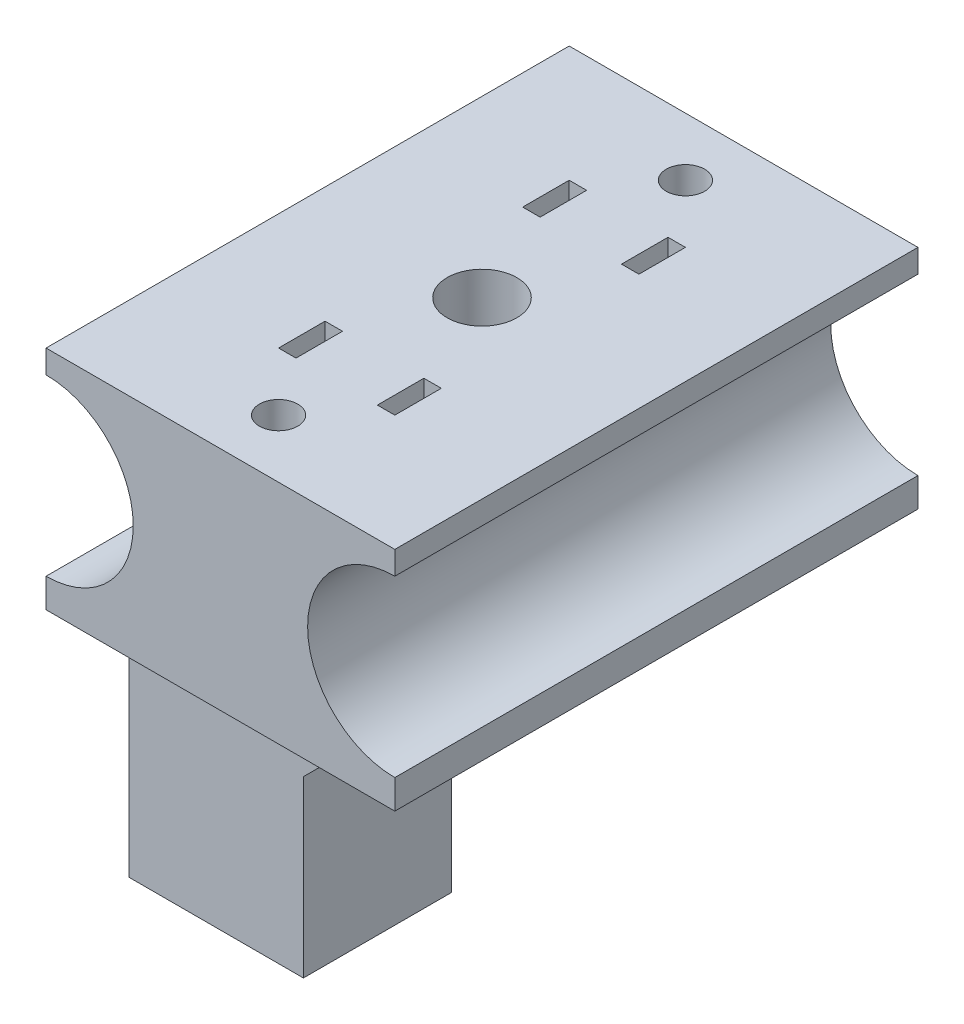
SolidWorks part; units mm, degrees
material "ABS"
ref_plane "Front Plane" through (0, 0, 0) normal (0, 0, 1) x (1, 0, 0)
ref_plane "Top Plane" through (0, 0, 0) normal (0, 1, 0) x (1, 0, 0)
ref_plane "Right Plane" through (0, 0, 0) normal (1, 0, 0) x (0, 0, -1)
sketch "Sketch1" plane through (0, 0, 0) normal (0, 0, 1) x (1, 0, 0)
  line L0 (15, 0) -> (-15, 0) construction
  line L5 (-15, 7.5) -> (-15, 9.5)
  line L6 (-15, 9.5) -> (15, 9.5)
  line L7 (15, 7.5) -> (15, 9.5)
  line L9 (-15, -7.5) -> (-15, -10)
  line L10 (-15, -10) -> (15, -10)
  line L11 (15, -7.5) -> (15, -10)
  arc A0 (15, 7.5) -> (15, -7.5) centre (15, 0) ccw
  arc A1 (-15, -7.5) -> (-15, 7.5) centre (-15, 0) ccw
  point P8 (0, 0)
  dimension "D2" = 15
  dimension "D1" = 30
  dimension "D3" = 2.5
  dimension "D4" = 2
extrude "Boss-Extrude1" add sketch "Sketch1" along normal mid plane 45
sketch "Sketch3" plane through (0, 0, 0) normal (0, 0, 1) x (1, 0, 0)
  line L0 (0, 9.5) -> (0, -10)
  line L1 (0, -10) -> (8, -10)
  line L2 (8, -10) -> (8, -3.25)
  line L3 (8, -3.25) -> (6, -3.25)
  line L4 (6, -3.25) -> (6, 2.75)
  line L5 (6, 2.75) -> (8, 2.75)
  line L6 (8, 2.75) -> (8, 9.5)
  line L7 (8, 9.5) -> (0, 9.5)
  line L8 (15, 9.5) -> (-15, 9.5) construction
  line L9 (-15, -10) -> (15, -10) construction
  dimension "D1" = 6
  dimension "D2" = 8
  dimension "D3" = 6
revolve "Cut-Revolve1" [suppressed] cut sketch "Sketch3" angle 360 about L0
hole_wizard "M4x0.7 Tapped Hole2" positions "Sketch5" profile "Sketch4" tap size "M4x0.7" standard "ANSI Metric" end condition through all
sketch "Sketch5" plane through (0, -10, 0) normal (0, -1, 0) x (-1, 0, 0)
  line L0 (0, 17.5) -> (0, -17.5) construction
  line L2 (15, -22.5) -> (-15, -22.5) construction
  point P0 (0, -17.5)
  point P2 (0, 17.5)
  dimension "D1" = 5
sketch "Sketch4" plane through (0, -10, 17.5) normal (1, 0, 0) x (0, 0, -1)
  line L0 (0, 0) -> (0, 19.5)
  line L1 (0, 19.5) -> (1.65, 19.5)
  line L2 (1.65, 19.5) -> (1.65, 0)
  line L5 (1.65, 0) -> (0, 0)
  line L11 (0, -6.35) -> (0, 107.95) construction
  dimension "Thru Tap Drill Dia." = 3.3
  dimension "Thru Tap Drill Depth" = 19.5
cosmetic thread "Hole Thread1" parameters "D2"=4
cosmetic thread "Hole Thread2" parameters "D2"=4
sketch "Sketch7" plane through (0, 0, 0) normal (0, 0, 1) x (1, 0, 0)
  line L0 (-15, -7.5) -> (-24, -7.5)
  line L1 (-24, -7.5) -> (-24, -42.5)
  line L5 (8.5, -10) -> (-15, -10)
  line L6 (-15, -10) -> (-15, -7.5)
  line L7 (-24, -42.5) -> (-9, -42.5)
  line L8 (-9, -42.5) -> (-9, -27.5)
  line L9 (-9, -27.5) -> (8.5, -10)
  dimension "D1" = 9
  dimension "D2" = 35
  dimension "D3" = 15
  dimension "D4" = 45
  dimension "D6" = 15
extrude "Boss-Extrude3" add sketch "Sketch7" against normal mid plane 12.725
hole_wizard "M4x0.7 Tapped Hole1" positions "Sketch9" profile "Sketch8" tap size "M4x0.7" standard "ANSI Metric"
sketch "Sketch9" plane through (-24, 0, 0) normal (1, 0, 0) x (0, 0, -1)
  line L0 (6.3625, -42.5) -> (-6.3625, -42.5) construction
  point P0 (0, -37.5)
  point P2 (0, -22.5)
  dimension "D1" = 15
  dimension "D2" = 5
sketch "Sketch8" plane through (-24, -37.5, 0) normal (0, 1, 0) x (0, 0, 1)
  line L0 (0, 0) -> (0, 10.9914)
  line L1 (0, 10.9914) -> (1.65, 10)
  line L2 (1.65, 10) -> (1.65, 0)
  line L5 (1.65, 0) -> (0, 0)
  line L10 (0, 10.9914) -> (-1.65, 10) construction
  line L11 (0, -6.35) -> (0, 107.95) construction
  dimension "Tap Drill Dia." = 3.3
  dimension "Tap Drill Depth" = 10
  dimension "Drill Angle" = 118
cosmetic thread "Hole Thread5" parameters "D1"=8, "D2"=4
cosmetic thread "Hole Thread6" parameters "D1"=8, "D2"=4
sketch "Sketch10" plane through (0, 0, -6.3625) normal (0, 0, -1) x (-1, 0, 0)
  line L0 (15, -10) -> (24, -19)
  line L1 (24, -7.5) -> (24, -42.5) construction
  line L2 (24, -19) -> (24, -7.5)
  line L3 (24, -7.5) -> (15, -7.5)
  line L4 (15, -7.5) -> (15, -10)
  dimension "D1" = 45
extrude "Cut-Extrude2" cut sketch "Sketch10" against normal blind 85
sketch "Sketch2" plane through (0, 9.5, 0) normal (0, 1, 0) x (1, 0, 0)
  circle A0 centre (0, 0) radius 3
  dimension "D1" = 6
extrude "Cut-Extrude1" cut sketch "Sketch2" against normal blind 50
sketch "Sketch11" plane through (0, 0, -22.5) normal (0, 0, -1) x (-1, 0, 0)
  line L0 (-5, 9.5) -> (-5, 0)
  line L1 (-15, 9.5) -> (15, 9.5) construction
  line L3 (-15, -10) -> (-3.5, -10)
  line L4 (15, -10) -> (-15, -10) construction
  line L5 (-3.5, -10) -> (-3.5, 9.5)
  line L6 (-3.5, 9.5) -> (-5, 9.5)
  line L7 (0, 9.5) -> (0, -10) construction
  line L8 (3.5, 9.5) -> (5, 9.5)
  line L9 (3.5, -10) -> (3.5, 9.5)
  line L10 (15, -10) -> (3.5, -10)
  line L11 (5, 9.5) -> (5, 0)
  arc A0 (-5, 0) -> (-15, -10) centre (-15, 0) cw
  arc A1 (5, 0) -> (15, -10) centre (15, 0) ccw
  arc A3 (-15, -7.5) -> (-15, 7.5) centre (-15, 0) ccw construction
  line M5 (-15, -7.5) -> (-15, -10)
  line M6 (-15, -10) -> (15, -10)
  line M7 (15, -10) -> (15, -7.5)
  line M10 (15, 9.5) -> (-15, 9.5)
  dimension "D2" = 1.5
extrude "Cut-Extrude3" cut sketch "Sketch11" against normal blind 4 from offset 10 contours A1 L11 L9 M10 M6 M7 | L0 A0 L5 M5 M6 M10 offset against normal yes
mirror "Mirror1" about plane through (0, 0, 0) normal (0, 0, 1) of "Cut-Extrude3"
